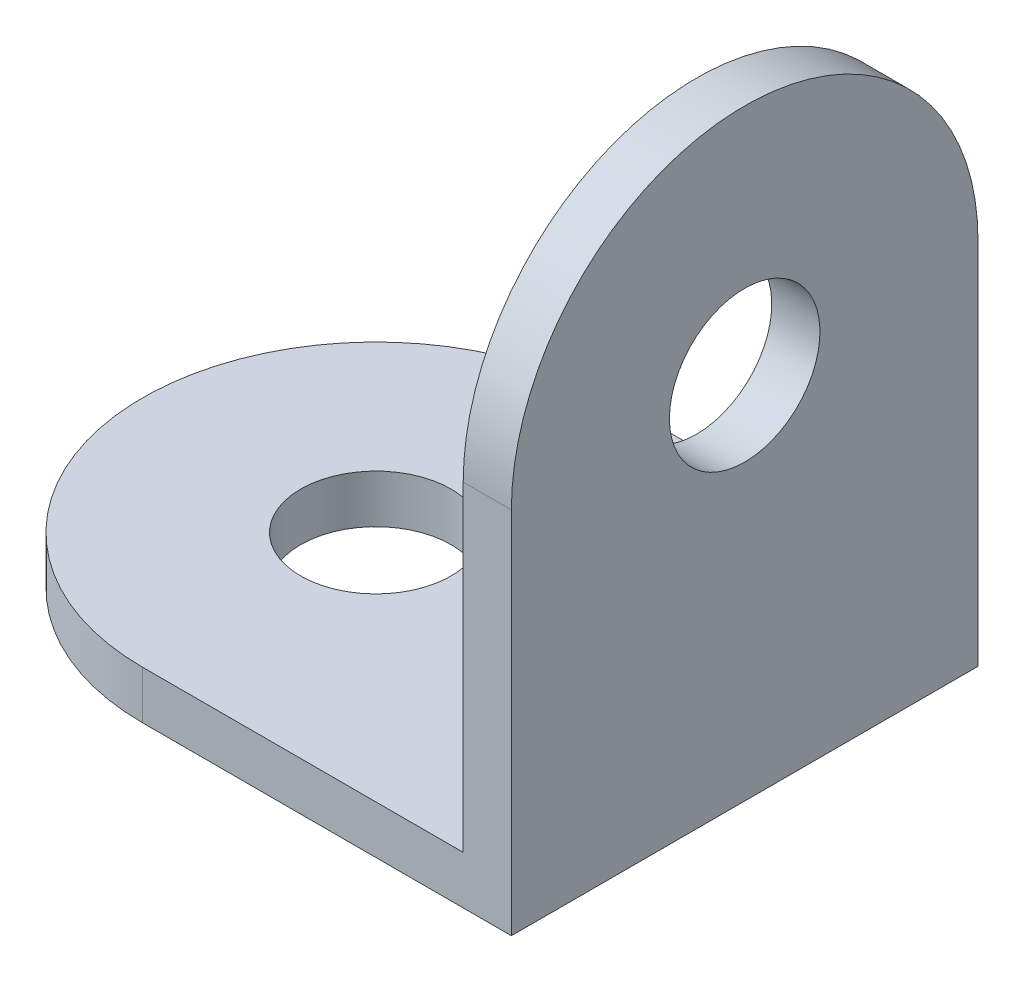
SolidWorks part; units mm, degrees
ref_plane "前视基准面" through (0, 0, 0) normal (0, 0, 1) x (1, 0, 0)
ref_plane "上视基准面" through (0, 0, 0) normal (0, 1, 0) x (1, 0, 0)
ref_plane "右视基准面" through (0, 0, 0) normal (1, 0, 0) x (0, 0, -1)
other "Configuration Table"
sketch "草图1" plane through (0, 0, 0) normal (0, 0, 1) x (1, 0, 0)
  line L0 (0, 0) -> (-20, 0)
  line L1 (0, 0) -> (0, 20)
  line L2 (0, 20) -> (-1.6, 20)
  line L3 (-1.6, 20) -> (-1.6, 1.6)
  line L4 (-1.6, 1.6) -> (-20, 1.6)
  line L5 (-20, 1.6) -> (-20, 0)
  dimension "D1" = 1.6
  dimension "D2" = 20
  dimension "D3" = 20
extrude "凸台-拉伸1" add sketch "草图1" along normal blind 15.5
sketch "草图2" plane through (-1.6, 0, 0) normal (-1, 0, 0) x (0, 0, 1)
  line L0 (0, 20) -> (0, 1.6) construction
  line L1 (15.5, 20) -> (15.5, 1.6) construction
  line L2 (15.5, 20) -> (0, 20) construction
  line L3 (0, 12.25) -> (0, 20)
  line L4 (0, 20) -> (15.5, 20)
  line L5 (15.5, 20) -> (15.5, 12.25)
  circle A0 centre (7.75, 12.25) radius 7.75
  line M1 (0, 20) -> (0, 1.6)
  line M3 (15.5, 1.6) -> (15.5, 20)
  line M4 (15.5, 20) -> (0, 20)
extrude "切除-拉伸1" cut sketch "草图2" against normal blind 15.5 contours A0 L4 M1 | A0 M3 M4
sketch "草图3" plane through (0, 1.6, 0) normal (0, 1, 0) x (1, 0, 0)
  line L0 (-20, -15.5) -> (-20, 0) construction
  line L1 (-1.6, -15.5) -> (-20, -15.5) construction
  line L2 (-1.6, 0) -> (-20, 0) construction
  line L3 (-12.25, 0) -> (-20, 0)
  line L4 (-20, 0) -> (-20, -15.5)
  line L5 (-20, -15.5) -> (-12.25, -15.5)
  circle A0 centre (-12.25, -7.75) radius 7.75
  line M1 (-1.6, 0) -> (-20, 0)
  line M2 (-20, 0) -> (-20, -15.5)
  line M3 (-20, -15.5) -> (-1.6, -15.5)
extrude "切除-拉伸2" cut sketch "草图3" against normal blind 15.5 contours A0 L4 M3 | A0 M1 M2
sketch "草图4" plane through (-1.6, 0, 0) normal (-1, 0, 0) x (0, 0, 1)
  circle A0 centre (7.75, 12.25) radius 2.5
  point P2 (7.75, 17.25)
  dimension "D1" = 5
extrude "切除-拉伸3" cut sketch "草图4" against normal blind 15.5
sketch "草图5" plane through (0, 1.6, 0) normal (0, 1, 0) x (1, 0, 0)
  circle A0 centre (-12.25, -7.75) radius 2.5
  point P2 (-17.25, -7.75)
  dimension "D1" = 5
extrude "切除-拉伸4" cut sketch "草图5" against normal blind 15.5
